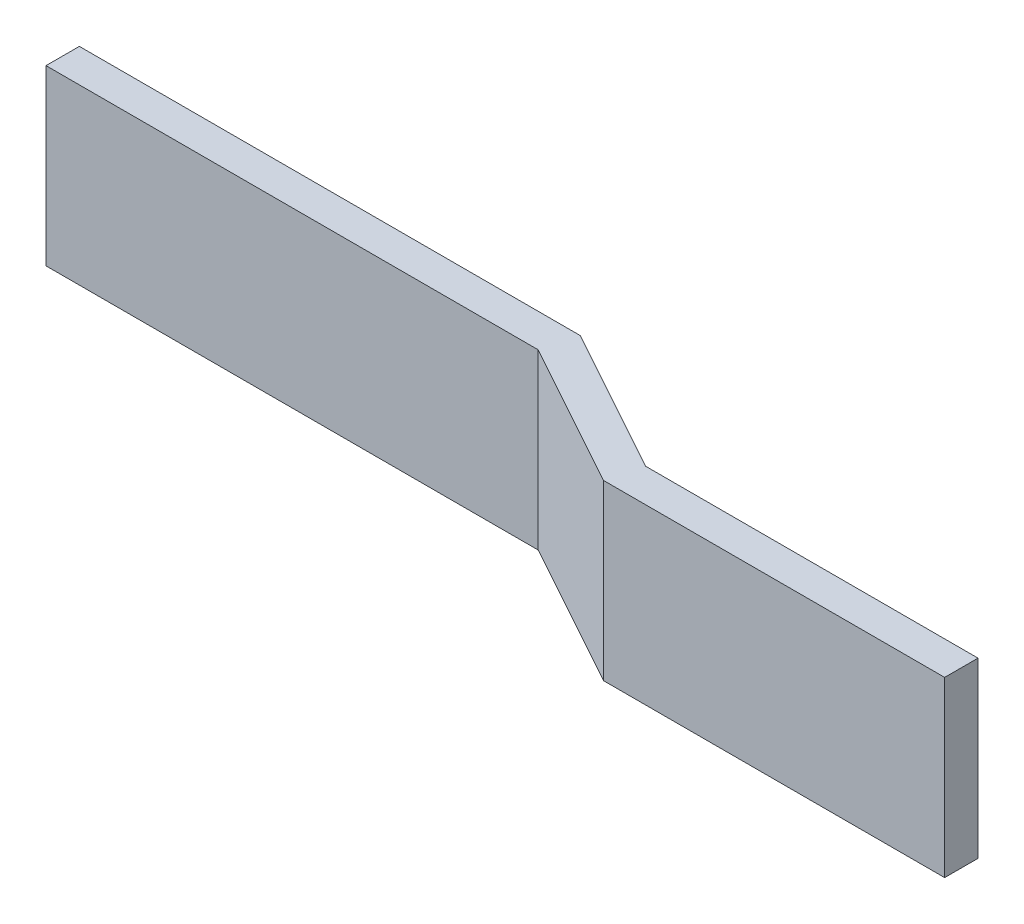
SolidWorks part; units mm, degrees
ref_plane "Front Plane" through (0, 0, 0) normal (0, 0, 1) x (1, 0, 0)
ref_plane "Top Plane" through (0, 0, 0) normal (0, 1, 0) x (1, 0, 0)
ref_plane "Right Plane" through (0, 0, 0) normal (1, 0, 0) x (0, 0, -1)
sketch "Sketch1" plane through (0, 0, 0) normal (0, 1, 0) x (1, 0, 0)
  line L0 (0, 0) -> (38.1391, 0)
  line L1 (38.1391, 0) -> (49.2453, -6.1289)
  line L2 (49.2453, -6.1289) -> (74.5674, -6.1289)
extrude "Extrude-Thin1" add sketch "Sketch1" along normal blind 13.208 thin
sketch "Sketch3" plane through (0, 0, 0) normal (0, 0, -1) x (-1, 0, 0)
  circle A0 centre (-6.1106, 6.604) radius 3.048
extrude "Cut-Extrude1" cut sketch "Sketch3" against normal blind 1.27
